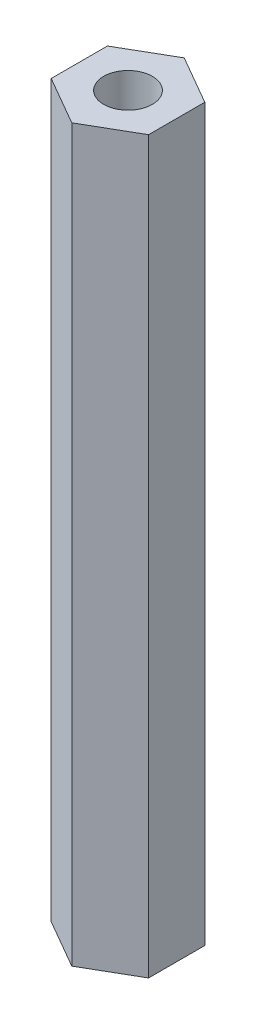
SolidWorks part; units mm, degrees
material "Brass"
ref_plane "Front Plane" through (0, 0, 0) normal (0, 0, 1) x (1, 0, 0)
ref_plane "Top Plane" through (0, 0, 0) normal (0, 1, 0) x (1, 0, 0)
ref_plane "Right Plane" through (0, 0, 0) normal (1, 0, 0) x (0, 0, -1)
sketch "Sketch1" plane through (0, 0, 0) normal (0, 1, 0) x (1, 0, 0)
  line L1 (3, -1.7321) -> (3, 1.7321)
  line L2 (3, 1.7321) -> (0, 3.4641)
  line L3 (0, 3.4641) -> (-3, 1.7321)
  line L4 (-3, 1.7321) -> (-3, -1.7321)
  line L5 (-3, -1.7321) -> (0, -3.4641)
  line L6 (0, -3.4641) -> (3, -1.7321)
  circle A0 centre (0, 0) radius 3 construction
  circle A1 centre (0, 0) radius 1.5
  point P10 (0, 0)
  dimension "D1" = 6
  dimension "D2" = 3
extrude "Boss-Extrude2" add sketch "Sketch1" along normal blind 45
